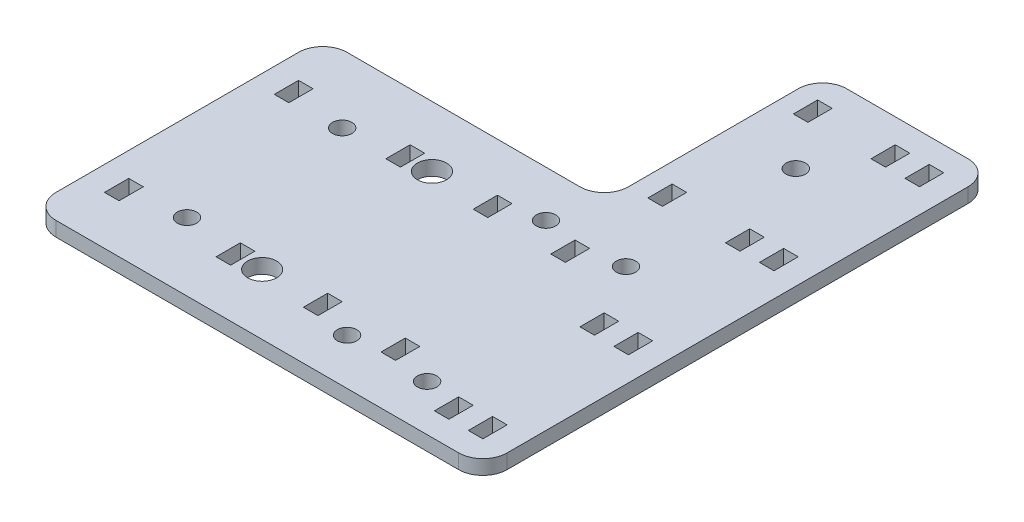
SolidWorks part; units mm, degrees
ref_plane "Front Plane" through (0, 0, 0) normal (0, 0, 1) x (1, 0, 0)
ref_plane "Top Plane" through (0, 0, 0) normal (0, 1, 0) x (1, 0, 0)
ref_plane "Right Plane" through (0, 0, 0) normal (1, 0, 0) x (0, 0, -1)
sketch "Sketch1" plane through (0, 0, 0) normal (0, 1, 0) x (1, 0, 0)
  line L1 (0, 0) -> (93, 0)
  line L2 (0, 0) -> (0, 60)
  line L3 (0, 60) -> (93, 60)
  line L4 (93, 0) -> (93, 60)
  dimension "D1" = 60
  dimension "D2" = 93
extrude "Boss-Extrude1" add sketch "Sketch1" along normal blind 3
ref_plane "Plane1" through (0, 0, -30) normal (0, 0, 1) x (1, 0, 0)
sketch "Sketch2" plane through (0, 3, 0) normal (0, 1, 0) x (1, 0, 0)
  line L0 (0, 60) -> (0, 0) construction
  line L1 (65, 10) -> (62, 10)
  line L2 (65, 10) -> (65, 15)
  line L3 (65, 15) -> (62, 15)
  line L4 (62, 10) -> (62, 15)
  line L9 (49, 10) -> (46, 10)
  line L10 (49, 10) -> (49, 15)
  line L11 (49, 15) -> (46, 15)
  line L12 (46, 10) -> (46, 15)
  line L13 (31, 10) -> (28, 10)
  line L14 (31, 10) -> (31, 15)
  line L15 (31, 15) -> (28, 15)
  line L16 (28, 10) -> (28, 15)
  line L17 (8, 10) -> (5, 10)
  line L18 (8, 10) -> (8, 15)
  line L19 (8, 15) -> (5, 15)
  line L20 (5, 10) -> (5, 15)
  line L21 (0, 0) -> (93, 0) construction
  dimension "D1" = 3
  dimension "D3" = 3
  dimension "D4" = 3
  dimension "D5" = 3
  dimension "D8" = 15
  dimension "D9" = 20
  dimension "D10" = 5
  dimension "D11" = 10
  dimension "D12" = 5
extrude "Cut-Extrude1" cut sketch "Sketch2" against normal blind 3
mirror "Mirror1" about plane through (0, 0, -30) normal (0, 0, 1) of "Cut-Extrude1"
sketch "Sketch4" plane through (0, 0, -60) normal (0, 0, -1) x (-1, 0, 0)
  line L0 (-93, 3) -> (0, 3) construction
  line L1 (-93, 3) -> (-58, 3)
  line L2 (-93, 3) -> (-93, 0)
  line L3 (-93, 0) -> (-58, 0)
  line L4 (-58, 3) -> (-58, 0)
  line L5 (-93, 0) -> (0, 0) construction
  dimension "D1" = 35
extrude "Boss-Extrude2" add sketch "Sketch4" along normal blind 45
sketch "Sketch5" plane through (0, 3, 0) normal (0, 1, 0) x (1, 0, 0)
  line L0 (93, 0) -> (93, 105) construction
  line L1 (88, 10) -> (85, 10)
  line L2 (88, 10) -> (88, 5)
  line L3 (88, 5) -> (85, 5)
  line L4 (85, 10) -> (85, 5)
  line L5 (81, 10) -> (78, 10)
  line L6 (81, 10) -> (81, 5)
  line L7 (81, 5) -> (78, 5)
  line L8 (78, 10) -> (78, 5)
  line L11 (-1.65, 0) -> (1.65, 0) construction
  dimension "D1" = 3
  dimension "D2" = 5
  dimension "D3" = 4
  dimension "D4" = 3
  dimension "D5" = 5
  dimension "D6" = 5
fillet "Fillet1" radius 5 6 edges at (93, 1.5, 0) (0, 1.5, -60) (0, 1.5, 0) (93, 1.5, -105) (58, 1.5, -105) (58, 1.5, -60)
extrude "Cut-Extrude3" cut sketch "Sketch5" against normal through all
ref_plane "Plane5" through (0, 0, -7.5) normal (0, 0, -1) x (-1, 0, 0)
pattern_linear "LPattern1" count 4 spacing 30 along (0, 0, -1) count 2 spacing 30 of "Cut-Extrude3"
sketch "Sketch6" plane through (0, 3, 0) normal (0, 1, 0) x (1, 0, 0)
  line L0 (8, 10) -> (8, 15) construction
  line L1 (-1.65, 30) -> (1.65, 30) construction
  circle A0 centre (18, 14) radius 2
  circle A1 centre (18, 46) radius 2
  circle A2 centre (55.5, 50.5) radius 2
  circle A3 centre (55.5, 9.5) radius 2
  circle A4 centre (72, 9.5) radius 2
  circle A5 centre (72, 50.5) radius 2
  circle A6 centre (72, 85.5) radius 2
  point P6 (8, 12.5)
  dimension "D1" = 4
  dimension "D2" = 4
  dimension "D3" = 10
  dimension "D7" = 4
  dimension "D8" = 4
  dimension "D11" = 4
  dimension "D12" = 4
  dimension "D13" = 4
  dimension "D4" = 37.5
  dimension "D5" = 32
  dimension "D6" = 16
  dimension "D9" = 41
  dimension "D10" = 20.5
  dimension "D14" = 35
  dimension "D15" = 16.5
extrude "Cut-Extrude4" cut sketch "Sketch6" against normal through all
ref_plane "Plane6" through (0, 0, -60) normal (0, 0, -1) x (-1, 0, 0)
sketch "Sketch7" plane through (0, 3, 0) normal (0, 1, 0) x (1, 0, 0)
  line L0 (65, 50) -> (65, 45) construction
  line L1 (65, 65) -> (62, 65)
  line L2 (65, 65) -> (65, 70)
  line L3 (65, 70) -> (62, 70)
  line L4 (62, 65) -> (62, 70)
  line L5 (65, 95) -> (62, 95)
  line L6 (65, 95) -> (65, 100)
  line L7 (65, 100) -> (62, 100)
  line L8 (62, 95) -> (62, 100)
  line L9 (62, 45) -> (62, 50) construction
  line L10 (78, 65) -> (81, 65) construction
  line L11 (81, 70) -> (78, 70) construction
  line L12 (78, 95) -> (81, 95) construction
  line L13 (81, 100) -> (78, 100) construction
extrude "Cut-Extrude5" cut sketch "Sketch7" against normal through all
sketch "Sketch8" plane through (0, 3, 0) normal (0, 1, 0) x (1, 0, 0)
  line L0 (31, 50) -> (31, 45) construction
  line L2 (31, 45) -> (28, 45) construction
  circle A1 centre (35, 12.5) radius 3
  circle A2 centre (35, 47.5) radius 3
  point P6 (0, 0)
  point P9 (28, 45)
  dimension "D1" = 6
  dimension "D2" = 6
  dimension "D3" = 4
  dimension "D4" = 35
  dimension "D5" = 2.5
extrude "Cut-Extrude6" cut sketch "Sketch8" against normal through all
